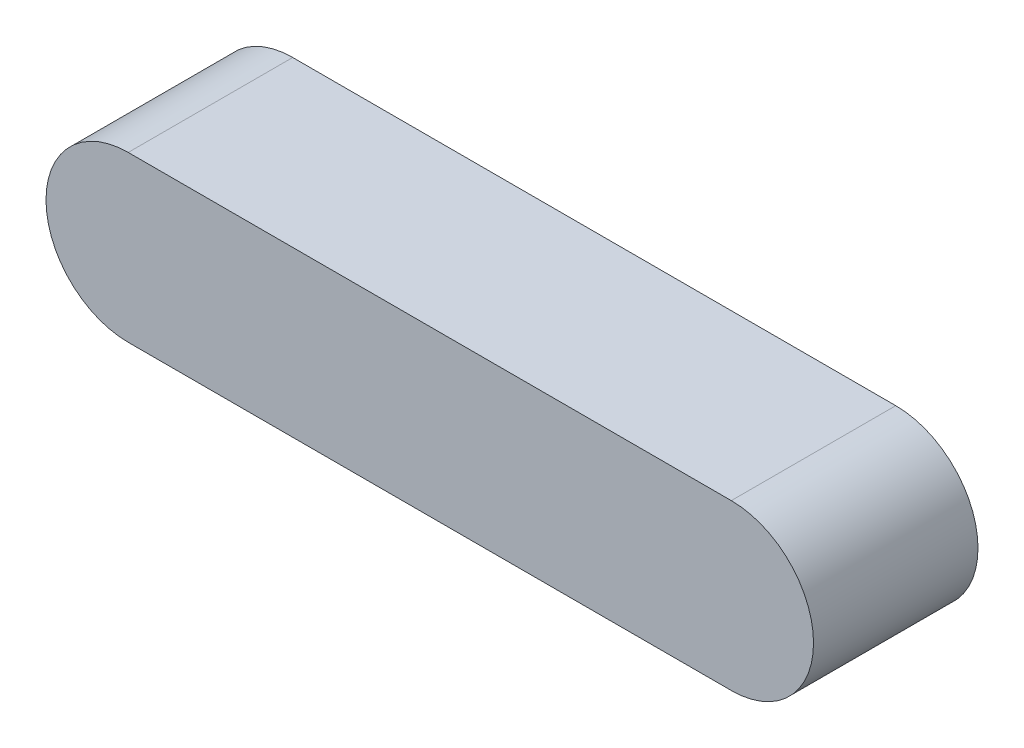
SolidWorks part; units mm, degrees
ref_plane "Plan de face" through (0, 0, 0) normal (0, 0, 1) x (1, 0, 0)
ref_plane "Plan de dessus" through (0, 0, 0) normal (0, 1, 0) x (1, 0, 0)
ref_plane "Plan de droite" through (0, 0, 0) normal (1, 0, 0) x (0, 0, -1)
sketch "Sketch1" plane through (0, 0, 0) normal (0, 0, 1) x (1, 0, 0)
  line L0 (-5.5, 0) -> (5.5, 0) construction
  line L1 (-5.5, 1.5) -> (5.5, 1.5)
  line L2 (-5.5, -1.5) -> (5.5, -1.5)
  arc A0 (-5.5, 1.5) -> (-5.5, -1.5) centre (-5.5, 0) ccw
  arc A1 (5.5, -1.5) -> (5.5, 1.5) centre (5.5, 0) ccw
  point P2 (0, 0)
  dimension "D2" = 1.5
  dimension "D1" = 11
extrude "Boss-Extrude1" add sketch "Sketch1" along normal blind 3
